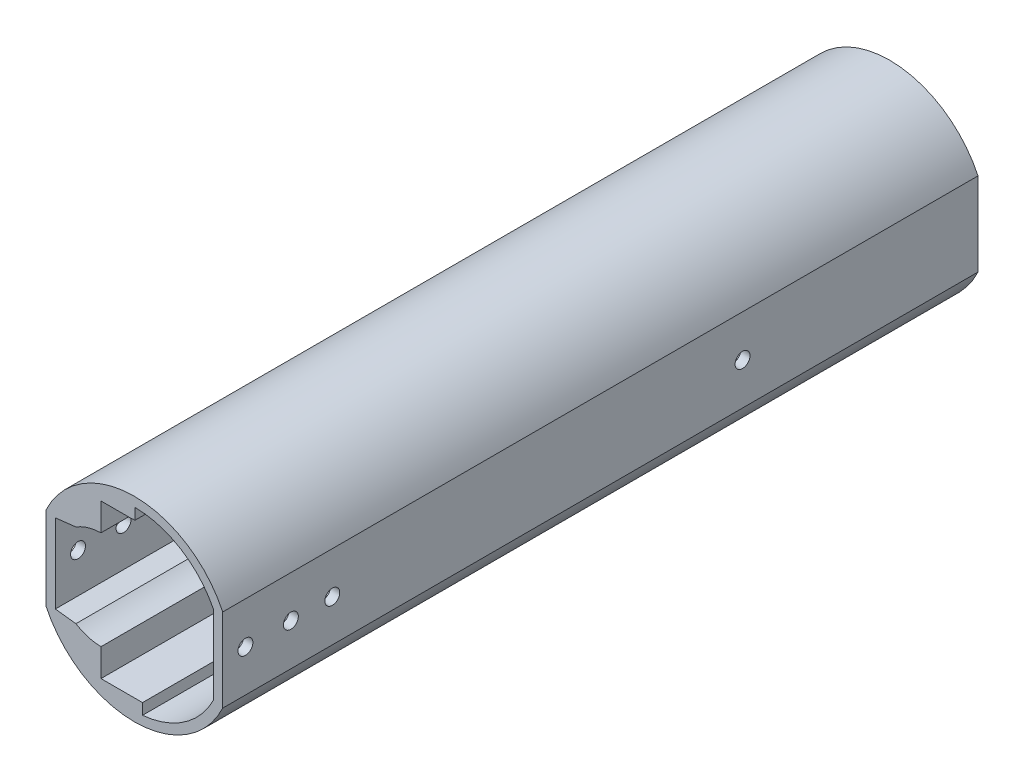
SolidWorks part; units mm, degrees
ref_plane "Front Plane" through (0, 0, 0) normal (0, 0, 1) x (1, 0, 0)
ref_plane "Top Plane" through (0, 0, 0) normal (0, 1, 0) x (1, 0, 0)
ref_plane "Right Plane" through (0, 0, 0) normal (1, 0, 0) x (0, 0, -1)
sketch "Sketch1" plane through (0, 0, 0) normal (0, 0, 1) x (1, 0, 0)
  line L1 (17.2, 8.8839) -> (17.2, -8.9822)
  line L2 (-1.75, -18.9991) -> (-1.75, 18.9008)
  line L3 (-20.6999, 8.8839) -> (-20.6999, -8.9822)
  line L5 (-18.6999, 8.4244) -> (-18.6999, -8.5226)
  line L6 (15.2, 8.4244) -> (15.2, -8.5226)
  arc A8 (15.2, 8.4244) -> (-18.6999, 8.4244) centre (-1.75, -0.0491) ccw
  arc A9 (17.2, 8.8839) -> (-20.6999, 8.8839) centre (-1.75, -0.0491) ccw
  arc A10 (-20.6999, -8.9822) -> (17.2, -8.9822) centre (-1.75, -0.0491) ccw
  circle A11 centre (-1.75, -0.0491) radius 18.95 construction
  circle A12 centre (-1.75, -0.0491) radius 20.95 construction
  arc A13 (-18.6999, -8.5226) -> (15.2, -8.5226) centre (-1.75, -0.0491) ccw
  point P4 (19.2, -0.0491)
  point P8 (17.2, 16.25)
  point P9 (17.2, -16.25)
  point P14 (15.2, 16.25)
  point P15 (15.2, -16.25)
  point P18 (17.2, -0.0491)
  dimension "D1" = 2
extrude "Boss-Extrude2" add sketch "Sketch1" against normal up to surface (95 mm away) contours L3 A10 L1 A9 A13 L5 A8 L6
sketch "Sketch2" plane through (0, 0, 0) normal (0, 0, 1) x (1, 0, 0)
  line L0 (-8.912, 8.9586) -> (-8.912, 9.1586)
  line L1 (-14.2788, 8.9325) -> (-18.6999, 8.4244)
  line L2 (-18.6999, -0.0491) -> (-16.4894, -0.0491)
  line L3 (-3.6, 16.45) -> (7.571, 16.45)
  line L4 (-18.6999, 8.4244) -> (-18.6999, -8.5226)
  line L5 (15.2, -8.5226) -> (15.2, 8.4244)
  line L6 (-18.6999, 8.4244) -> (-18.6999, -8.5226)
  line L7 (15.2, -8.5226) -> (15.2, 8.4244)
  line L8 (-8.712, 16.45) -> (-3.6, 16.45)
  line L9 (-8.712, 16.45) -> (-3.6, 16.45)
  line L10 (-8.712, 16.45) -> (-8.912, 16.45)
  line L11 (-8.712, -16.5483) -> (-8.912, -16.5483)
  line L12 (-8.912, 16.45) -> (-8.912, 16.25)
  line L13 (-8.912, 16.25) -> (-8.912, -16.25)
  line L14 (-8.912, 16.25) -> (-8.912, -16.25)
  line L15 (-3.6, -16.5483) -> (7.571, -16.5483)
  line L16 (-8.712, -16.5483) -> (-3.6, -16.5483)
  line L17 (-14.2788, -9.0307) -> (-18.6999, -8.5226)
  line L18 (-8.912, -16.25) -> (-8.912, -16.5483)
  arc A1 (-2.5876, 4.1335) -> (-10.2868, 9.1326) centre (-10.744, 0) ccw construction
  arc A3 (-8.712, -10.6234) -> (-14.2788, -9.0307) centre (-8.712, -0.0983) cw
  arc A4 (-18.6999, -8.5226) -> (15.2, -8.5226) centre (-1.75, -0.0491) ccw
  arc A5 (15.2, 8.4244) -> (-18.6999, 8.4244) centre (-1.75, -0.0491) ccw
  arc A6 (-18.6999, -8.5226) -> (15.2, -8.5226) centre (-1.75, -0.0491) ccw
  arc A7 (15.2, 8.4244) -> (-18.6999, 8.4244) centre (-1.75, -0.0491) ccw
  arc A8 (-8.712, 10.5251) -> (-14.2788, 8.9325) centre (-8.712, 0) ccw
  arc A9 (-8.712, 10.5251) -> (-14.2788, 8.9325) centre (-8.712, 0) ccw
  point P19 (-8.812, 16.45)
  point P20 (-8.812, -16.5483)
  dimension "D3" = 0.2
  dimension "D4" = 0.2
  dimension "D1" = 2
  dimension "D2" = 0.2
extrude "Boss-Extrude3" add sketch "Sketch2" against normal up to vertex (95 mm away) contours A9 L14 L12 L10 L9 L3 L1 M20 | L14 A3 L17 L15 L16 L11 L18 M18
sketch "Sketch3" plane through (0, 0, 0) normal (0, 0, 1) x (1, 0, 0)
  line L4 (0, -16.5483) -> (0, -18.9181)
  line L5 (-8.912, -16.5483) -> (7.571, -16.5483) construction
  line L6 (-18.6999, 8.4244) -> (-18.6999, -8.5226)
  line L7 (15.2, -8.5226) -> (15.2, 8.4244)
  line L8 (-18.6999, 8.4244) -> (-18.6999, -8.5226)
  line L9 (15.2, -8.5226) -> (15.2, 8.4244)
  line L10 (-1.6, 16.45) -> (-1.6, 18.9002)
  line L11 (7.571, 16.45) -> (-8.912, 16.45) construction
  line L14 (7.571, 16.45) -> (-8.912, 16.45)
  line L15 (7.571, 16.45) -> (-8.912, 16.45)
  line L17 (-8.912, -16.5483) -> (7.571, -16.5483)
  line L18 (-8.912, -16.5483) -> (7.571, -16.5483)
  arc A6 (-18.6999, -8.5226) -> (15.2, -8.5226) centre (-1.75, -0.0491) ccw
  arc A7 (15.2, 8.4244) -> (-18.6999, 8.4244) centre (-1.75, -0.0491) ccw
  arc A8 (-18.6999, -8.5226) -> (15.2, -8.5226) centre (-1.75, -0.0491) ccw
  arc A9 (15.2, 8.4244) -> (-18.6999, 8.4244) centre (-1.75, -0.0491) ccw
  dimension "D1" = 2
  dimension "D2" = 0
  dimension "D3" = 0
extrude "Cut-Extrude1" cut sketch "Sketch3" against normal through all contours L4 A8 M8 | A9 L10 M16
sketch "Sketch4" plane through (0, 0, 0) normal (0, 0, 1) x (1, 0, 0)
  line L4 (-20.6999, 8.8839) -> (-20.6999, -8.9822)
  line L5 (17.2, -8.9822) -> (17.2, 8.8839)
  line L6 (-20.6999, 8.8839) -> (-20.6999, -8.9822)
  line L7 (17.2, -8.9822) -> (17.2, 8.8839)
  line L180 (-18.6999, -8.5226) -> (-14.2788, -9.0307)
  line L181 (-8.912, -10.6215) -> (-8.912, -16.5483)
  line L182 (-8.912, -16.5483) -> (0, -16.5483)
  line L183 (0, -16.5483) -> (0, -18.9181)
  line L184 (15.2, -8.5226) -> (15.2, 8.4244)
  line L185 (-1.6, 18.9002) -> (-1.6, 16.45)
  line L186 (-1.6, 16.45) -> (-8.912, 16.45)
  line L187 (-8.912, 16.45) -> (-8.912, 10.5232)
  line L188 (-14.2788, 8.9325) -> (-18.6999, 8.4244)
  line L189 (-18.6999, 8.4244) -> (-18.6999, -8.5226)
  line L190 (-18.6999, -8.5226) -> (-14.2788, -9.0307)
  line L191 (-8.912, -10.6215) -> (-8.912, -16.5483)
  line L192 (-8.912, -16.5483) -> (0, -16.5483)
  line L193 (0, -16.5483) -> (0, -18.9181)
  line L194 (15.2, -8.5226) -> (15.2, 8.4244)
  line L195 (-1.6, 18.9002) -> (-1.6, 16.45)
  line L196 (-1.6, 16.45) -> (-8.912, 16.45)
  line L197 (-8.912, 16.45) -> (-8.912, 10.5232)
  line L198 (-14.2788, 8.9325) -> (-18.6999, 8.4244)
  line L199 (-18.6999, 8.4244) -> (-18.6999, -8.5226)
  arc A4 (-20.6999, -8.9822) -> (17.2, -8.9822) centre (-1.75, -0.0491) ccw
  arc A5 (17.2, 8.8839) -> (-20.6999, 8.8839) centre (-1.75, -0.0491) ccw
  arc A6 (-20.6999, -8.9822) -> (17.2, -8.9822) centre (-1.75, -0.0491) ccw
  arc A7 (17.2, 8.8839) -> (-20.6999, 8.8839) centre (-1.75, -0.0491) ccw
  arc A75 (-14.2788, -9.0307) -> (-8.912, -10.6215) centre (-8.712, -0.0983) ccw
  arc A76 (0, -18.9181) -> (15.2, -8.5226) centre (-1.75, -0.0491) ccw
  arc A77 (15.2, 8.4244) -> (-1.6, 18.9002) centre (-1.75, -0.0491) ccw
  arc A78 (-8.912, 10.5232) -> (-14.2788, 8.9325) centre (-8.712, 0) ccw
  arc A79 (-14.2788, -9.0307) -> (-8.912, -10.6215) centre (-8.712, -0.0983) ccw
  arc A80 (0, -18.9181) -> (15.2, -8.5226) centre (-1.75, -0.0491) ccw
  arc A81 (15.2, 8.4244) -> (-1.6, 18.9002) centre (-1.75, -0.0491) ccw
  arc A82 (-8.912, 10.5232) -> (-14.2788, 8.9325) centre (-8.712, 0) ccw
  dimension "D1" = 0
  dimension "D2" = 0
extrude "Boss-Extrude4" add sketch "Sketch4" along normal blind 20
sketch "Sketch5" plane through (0, 0, -95) normal (0, 0, -1) x (-1, 0, 0)
  line L4 (20.6999, -8.9822) -> (20.6999, 8.8839)
  line L5 (-17.2, 8.8839) -> (-17.2, -8.9822)
  line L6 (20.6999, -8.9822) -> (20.6999, 8.8839)
  line L7 (-17.2, 8.8839) -> (-17.2, -8.9822)
  line L89 (-15.2, 8.4244) -> (-15.2, -8.5226)
  line L90 (0, -18.9181) -> (0, -16.5483)
  line L91 (0, -16.5483) -> (8.912, -16.5483)
  line L92 (8.912, -16.5483) -> (8.912, -10.6215)
  line L93 (14.2788, -9.0307) -> (18.6999, -8.5226)
  line L94 (18.6999, -8.5226) -> (18.6999, 8.4244)
  line L95 (18.6999, 8.4244) -> (14.2788, 8.9325)
  line L96 (8.912, 10.5232) -> (8.912, 16.45)
  line L97 (8.912, 16.45) -> (1.6, 16.45)
  line L98 (1.6, 16.45) -> (1.6, 18.9002)
  line L99 (-15.2, 8.4244) -> (-15.2, -8.5226)
  line L100 (0, -18.9181) -> (0, -16.5483)
  line L101 (0, -16.5483) -> (8.912, -16.5483)
  line L102 (8.912, -16.5483) -> (8.912, -10.6215)
  line L103 (14.2788, -9.0307) -> (18.6999, -8.5226)
  line L104 (18.6999, -8.5226) -> (18.6999, 8.4244)
  line L105 (18.6999, 8.4244) -> (14.2788, 8.9325)
  line L106 (8.912, 10.5232) -> (8.912, 16.45)
  line L107 (8.912, 16.45) -> (1.6, 16.45)
  line L108 (1.6, 16.45) -> (1.6, 18.9002)
  arc A4 (20.6999, 8.8839) -> (-17.2, 8.8839) centre (1.75, -0.0491) ccw
  arc A5 (-17.2, -8.9822) -> (20.6999, -8.9822) centre (1.75, -0.0491) ccw
  arc A6 (20.6999, 8.8839) -> (-17.2, 8.8839) centre (1.75, -0.0491) ccw
  arc A7 (-17.2, -8.9822) -> (20.6999, -8.9822) centre (1.75, -0.0491) ccw
  arc A42 (-15.2, -8.5226) -> (0, -18.9181) centre (1.75, -0.0491) ccw
  arc A43 (8.912, -10.6215) -> (14.2788, -9.0307) centre (8.712, -0.0983) ccw
  arc A44 (14.2788, 8.9325) -> (8.912, 10.5232) centre (8.712, 0) ccw
  arc A45 (1.6, 18.9002) -> (-15.2, 8.4244) centre (1.75, -0.0491) ccw
  arc A46 (-15.2, -8.5226) -> (0, -18.9181) centre (1.75, -0.0491) ccw
  arc A47 (8.912, -10.6215) -> (14.2788, -9.0307) centre (8.712, -0.0983) ccw
  arc A48 (14.2788, 8.9325) -> (8.912, 10.5232) centre (8.712, 0) ccw
  arc A49 (1.6, 18.9002) -> (-15.2, 8.4244) centre (1.75, -0.0491) ccw
  dimension "D1" = 0
  dimension "D2" = 0
extrude "Boss-Extrude5" add sketch "Sketch5" along normal blind 45
sketch "Sketch6" plane through (0, 0, -140) normal (0, 0, -1) x (-1, 0, 0)
  line L4 (20.6999, -8.9822) -> (20.6999, 8.8839)
  line L5 (-17.2, 8.8839) -> (-17.2, -8.9822)
  line L6 (20.6999, -8.9822) -> (20.6999, 8.8839)
  line L7 (-17.2, 8.8839) -> (-17.2, -8.9822)
  arc A4 (-17.2, -8.9822) -> (20.6999, -8.9822) centre (1.75, -0.0491) ccw
  arc A5 (20.6999, 8.8839) -> (-17.2, 8.8839) centre (1.75, -0.0491) ccw
  arc A6 (-17.2, -8.9822) -> (20.6999, -8.9822) centre (1.75, -0.0491) ccw
  arc A7 (20.6999, 8.8839) -> (-17.2, 8.8839) centre (1.75, -0.0491) ccw
  dimension "D1" = 0
extrude "Boss-Extrude6" add sketch "Sketch6" along normal blind 2
sketch "Sketch7" plane through (0, 0, -142) normal (0, 0, -1) x (-1, 0, 0)
  line L0 (-17.2, 8.8839) -> (20.6999, -8.9822)
  line L1 (-17.2, -8.9822) -> (19.3145, 9.742)
  line L2 (0.3646, 0.8089) -> (0.3646, 21.7589)
  line L3 (0.3646, 0.8089) -> (12.6423, 0.8089)
  arc A0 (19.3145, 9.742) -> (-18.5854, 9.742) centre (0.3646, 0.8089) ccw construction
  circle A1 centre (1.6, 10.3251) radius 6.2
  circle A2 centre (1.6, -8.7072) radius 6.2
extrude "Cut-Extrude2" cut sketch "Sketch7" against normal through all contours L2 A1 | L2 A1 | A2
sketch "Sketch8" plane through (17.2, 0, 0) normal (1, 0, 0) x (0, 0, -1)
  line L8 (-20.2, -9.1822) -> (142.2, -9.1822)
  line L9 (142.2, -9.1822) -> (142.2, 9.0839)
  line L10 (142.2, 9.0839) -> (-20.2, 9.0839)
  line L11 (-20.2, 9.0839) -> (-20.2, -9.1822)
  line L12 (-20.2, -9.1822) -> (142.2, -9.1822)
  line L13 (142.2, -9.1822) -> (142.2, 9.0839)
  line L14 (142.2, 9.0839) -> (-20.2, 9.0839)
  line L15 (-20.2, 9.0839) -> (-20.2, -9.1822)
  dimension "D1" = 0.2
sketch "Sketch10" plane through (17.2, 0, 0) normal (1, 0, 0) x (0, 0, -1)
  line L4 (3.5, -0.0491) -> (5, -0.0491)
  circle A3 centre (91.5, -0.0491) radius 1.6
  circle A6 centre (3.5, -0.0491) radius 1.6
  circle A9 centre (-5.375, -0.0491) radius 1.6
  circle A12 centre (-15.125, -0.0246) radius 1.6
extrude "Cut-Extrude4" cut sketch "Sketch10" against normal through all
sketch "Sketch12" plane through (-20.6999, 0, 0) normal (-1, 0, 0) x (0, 0, 1)
  circle A2 centre (-91.5, -0.0491) radius 1.6
  circle A3 centre (-91.5, -0.0491) radius 1.6
  circle A5 centre (-3.5, -0.0491) radius 1.6
  circle A6 centre (-3.5, -0.0491) radius 1.6
  dimension "D1" = 0
  dimension "D2" = 0
extrude "Boss-Extrude8" add sketch "Sketch12" against normal up to surface (2 mm away) up to face at (-18.6999, -1.6246, 15.125)
